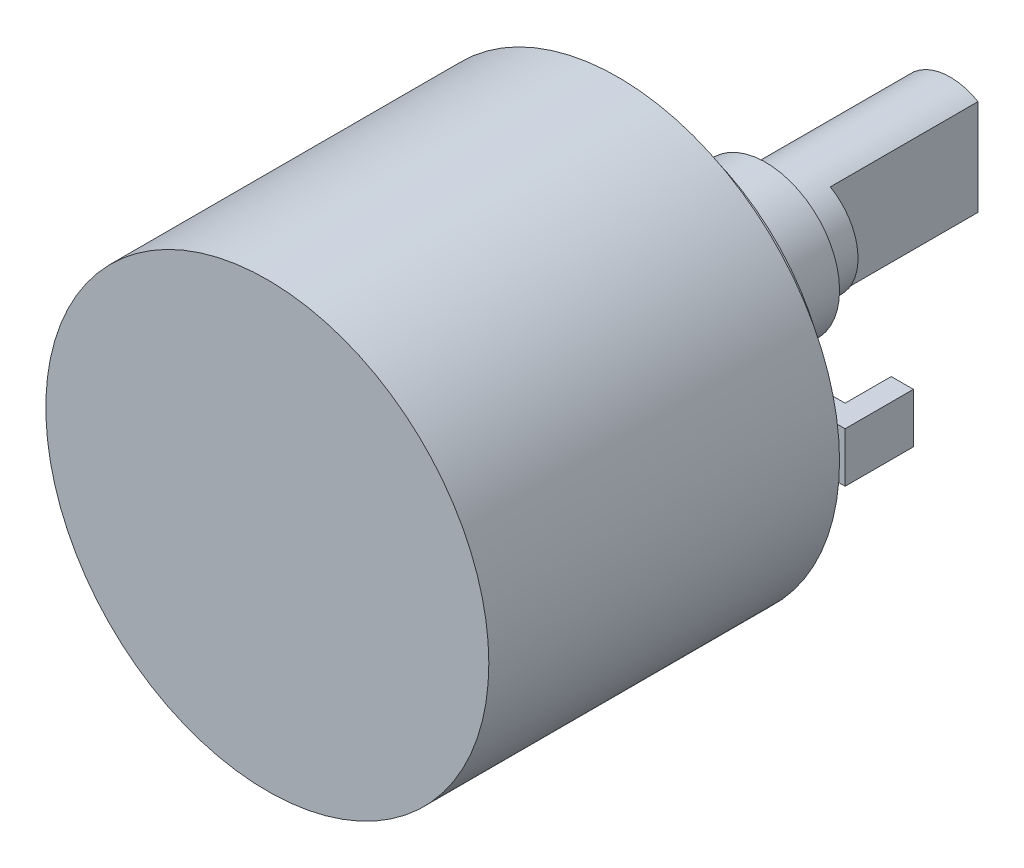
SolidWorks part; units mm, degrees
ref_plane "Спереди" through (0, 0, 0) normal (0, 0, 1) x (1, 0, 0)
ref_plane "Сверху" through (0, 0, 0) normal (0, 1, 0) x (1, 0, 0)
ref_plane "Справа" through (0, 0, 0) normal (1, 0, 0) x (0, 0, -1)
sketch "Эскиз1" plane through (0, 0, 0) normal (1, 0, 0) x (0, 0, -1)
  line L0 (-20.5, 0) -> (-20.5, 12)
  line L1 (-20.5, 12) -> (-1.5, 12)
  line L2 (-1.5, 12) -> (-1.5, 10)
  line L3 (-1.5, 10) -> (0, 10)
  line L4 (0, 10) -> (0, 4)
  line L5 (0, 4) -> (6.5, 4)
  line L6 (6.5, 4) -> (6.5, 3)
  line L7 (6.5, 3) -> (16.5, 3)
  line L8 (16.5, 3) -> (16.5, 0)
  line L9 (-20.5, 0) -> (16.5, 0) construction
  line L10 (-20.5, 0) -> (16.5, 0)
  point P8 (-0.75, 10)
  dimension "D1" = 24
  dimension "D2" = 20.5
  dimension "D3" = 1.5
  dimension "D4" = 6.5
  dimension "D5" = 10
  dimension "D6" = 6
  dimension "D7" = 8
  dimension "D8" = 20
revolve "Повернуть1" add sketch "Эскиз1" angle 360 about L9
sketch "Эскиз2" plane through (0, 0, 0) normal (0, 0, -1) x (-1, 0, 0)
  line L0 (0, 0) -> (-12, 0) construction
  line L2 (-12, 1.35) -> (-10.8, 1.35)
  line L3 (-12, 1.35) -> (-12, -1.35)
  line L4 (-12, -1.35) -> (-10.8, -1.35)
  line L5 (-10.8, 1.35) -> (-10.8, -1.35)
  point P7 (-12, 0)
  dimension "D1" = 2.7
  dimension "D2" = 1.2
  dimension "D3" = 12
extrude "Бобышка-Вытянуть1" add sketch "Эскиз2" along normal blind 2.5 separate body
sketch "Эскиз3" plane through (0, 0, 0) normal (0, 0, 1) x (1, 0, 0)
  line L0 (12, 1.35) -> (12, -1.35) construction
  line L1 (12, 1.35) -> (12, -1.35)
  line L2 (12, 1.35) -> (0, 1.35)
  line L3 (0, 1.35) -> (0, -1.35)
  line L4 (0, -1.35) -> (12, -1.35)
extrude "Бобышка-Вытянуть2" add sketch "Эскиз3" along normal blind 1.2
sketch "Эскиз4" plane through (0, 0, -16.5) normal (0, 0, -1) x (-1, 0, 0)
  line L0 (-1.5, 2.5981) -> (-1.5, -2.5981)
  arc A0 (-1.5, 2.5981) -> (-1.5, -2.5981) centre (0, 0) ccw
  circle A2 centre (0, 0) radius 3 construction
  dimension "D1" = 4.5
extrude "Вырез-Вытянуть1" cut sketch "Эскиз4" against normal offset from surface (8 mm away) 2 up to face at (4, 0, -6.5)
